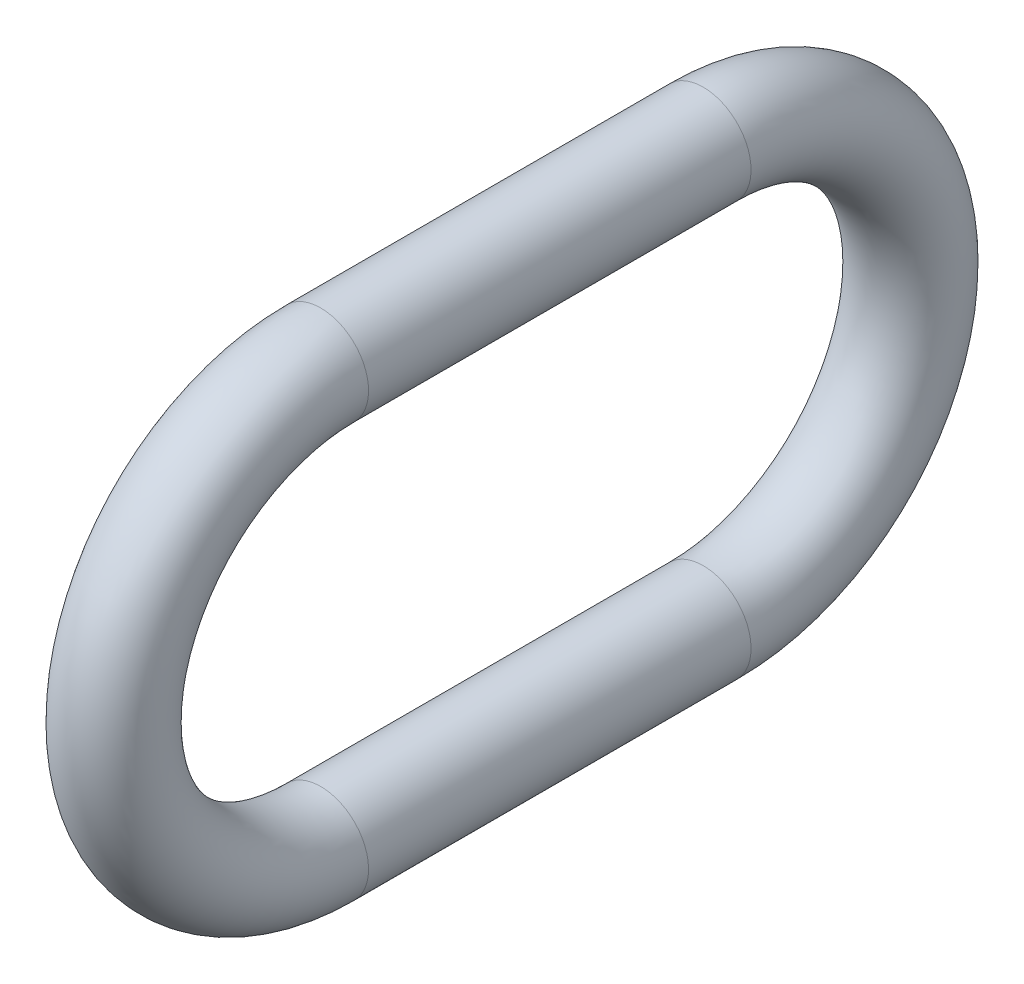
SolidWorks part; units mm, degrees
material "PE High Density"
ref_plane "Front Plane" through (0, 0, 0) normal (0, 0, 1) x (1, 0, 0)
ref_plane "Top Plane" through (0, 0, 0) normal (0, 1, 0) x (1, 0, 0)
ref_plane "Right Plane" through (0, 0, 0) normal (1, 0, 0) x (0, 0, -1)
sketch "Sketch1" plane through (0, 0, 0) normal (1, 0, 0) x (0, 0, -1)
  line L1 (31.75, -10.3187) -> (12.7, -10.3187)
  line L2 (31.75, -10.3187) -> (31.75, 10.3187) construction
  line L3 (31.75, 10.3187) -> (12.7, 10.3187)
  line L4 (12.7, -10.3187) -> (12.7, 10.3187) construction
  line L5 (22.225, 10.3187) -> (22.225, -10.3187) construction
  line L6 (31.75, 0) -> (12.7, 0) construction
  arc A0 (12.7, 10.3187) -> (12.7, -10.3187) centre (12.7, 0) ccw
  arc A1 (31.75, 10.3187) -> (31.75, -10.3187) centre (31.75, 0) cw
  circle A2 centre (31.75, 0) radius 12.7 construction
  circle A3 centre (31.75, 0) radius 7.9375 construction
  circle A4 centre (12.7, 0) radius 12.7 construction
  point P0 (22.225, 0)
  point P6 (44.45, 0)
  point P7 (0, 0)
  point P11 (31.75, -12.7)
  point P12 (31.75, 12.7)
  dimension "D3" = 4.7625
  dimension "D4" = 2.3812
  dimension "D1" = 44.45
  dimension "D2" = 25.4
sweep "Sweep1" add path "Sketch1" circular profile diameter 4.7625 parameters "D3"=4.7625
ref_plane "Plane1" through (0, 0, -44.45) normal (0, 0, 1) x (1, 0, 0)
